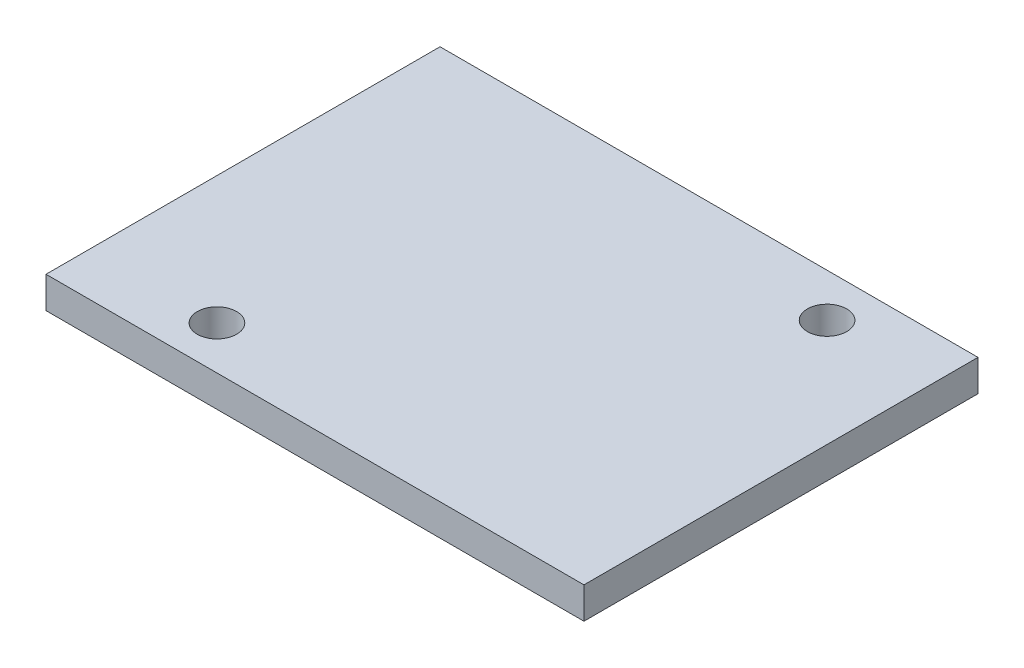
SolidWorks part; units mm, degrees
ref_plane "Front Plane" through (0, 0, 0) normal (0, 0, 1) x (1, 0, 0)
ref_plane "Top Plane" through (0, 0, 0) normal (0, 1, 0) x (1, 0, 0)
ref_plane "Right Plane" through (0, 0, 0) normal (1, 0, 0) x (0, 0, -1)
sketch "Sketch1" plane through (0, 0, 0) normal (0, 1, 0) x (1, 0, 0)
  line L1 (-13.6525, 10) -> (13.6525, 10)
  line L2 (-13.6525, 10) -> (-13.6525, -10)
  line L3 (-13.6525, -10) -> (13.6525, -10)
  line L4 (13.6525, 10) -> (13.6525, -10)
  line L5 (-13.6525, 10) -> (13.6525, -10) construction
  line L6 (-13.6525, -10) -> (13.6525, 10) construction
  point P0 (0, 0)
  dimension "D1" = 27.305
  dimension "D2" = 20
extrude "Boss-Extrude1" add sketch "Sketch1" along normal blind 1.6002
sketch "Sketch2" plane through (0, 1.6002, 0) normal (0, 1, 0) x (1, 0, 0)
  line L0 (-13.6525, -10) -> (-7.1755, -10) construction
  line L1 (-13.6525, -10) -> (13.6525, -10) construction
  line L2 (-7.1755, -10) -> (-7.1755, -7.8) construction
  line L3 (-7.1755, -7.8) -> (8.1915, -7.8) construction
  line L4 (-13.6525, 10) -> (-13.6525, -10) construction
  line L5 (13.6525, 10) -> (-13.6525, 10) construction
  circle A0 centre (-7.1755, -7.8) radius 1
  circle A1 centre (8.1915, 7.8) radius 1
  dimension "D1" = 2
  dimension "D4" = 2
  dimension "D2" = 6.477
  dimension "D3" = 2.2
  dimension "D5" = 15.367
  dimension "D6" = 2.2
extrude "Cut-Extrude1" cut sketch "Sketch2" against normal blind 1.6002
